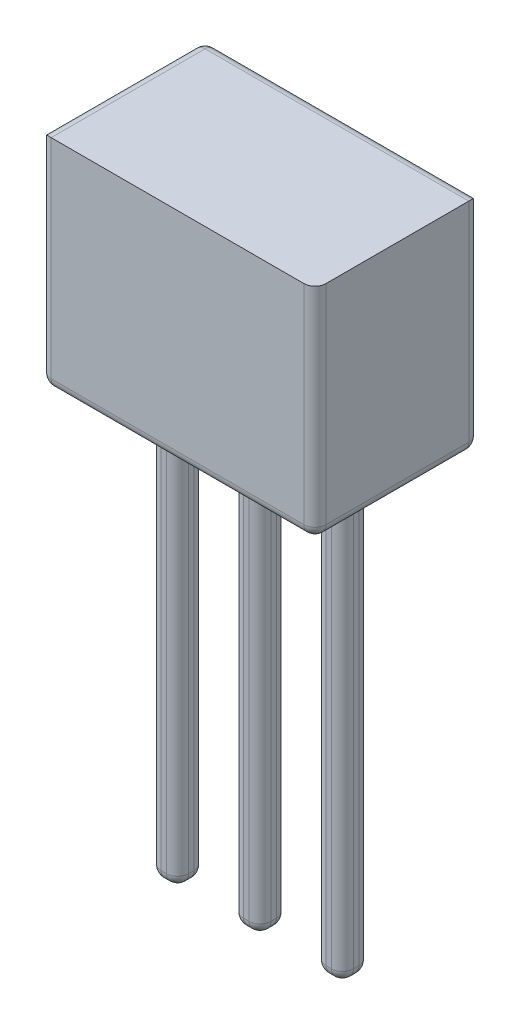
SolidWorks part; units mm, degrees
ref_plane "Front Plane" through (0, 0, 0) normal (0, 0, 1) x (1, 0, 0)
ref_plane "Top Plane" through (0, 0, 0) normal (0, 1, 0) x (1, 0, 0)
ref_plane "Right Plane" through (0, 0, 0) normal (1, 0, 0) x (0, 0, -1)
sketch "Sketch1" plane through (0, 0, 0) normal (0, 0, 1) x (1, 0, 0)
  line L1 (-50.1869, 22.1528) -> (-45.1869, 22.1528)
  line L2 (-50.1869, 22.1528) -> (-50.1869, 18.1528)
  line L3 (-50.1869, 18.1528) -> (-45.1869, 18.1528)
  line L4 (-45.1869, 22.1528) -> (-45.1869, 18.1528)
  line L5 (-50.1869, 22.1528) -> (-45.1869, 18.1528) construction
  line L6 (-50.1869, 18.1528) -> (-45.1869, 22.1528) construction
  point P0 (-47.6869, 20.1528)
  dimension "D1" = 4
  dimension "D2" = 5
extrude "Boss-Extrude1" add sketch "Sketch1" along normal blind 3
sketch "Sketch2" plane through (0, 18.1528, 0) normal (0, -1, 0) x (1, 0, 0)
  line L1 (-49.4369, 1.75) -> (-48.9369, 1.75)
  line L2 (-49.4369, 1.75) -> (-49.4369, 1.25)
  line L3 (-49.4369, 1.25) -> (-48.9369, 1.25)
  line L4 (-48.9369, 1.75) -> (-48.9369, 1.25)
  line L5 (-47.9369, 1.75) -> (-47.4369, 1.75)
  line L6 (-47.9369, 1.75) -> (-47.9369, 1.25)
  line L7 (-47.9369, 1.25) -> (-47.4369, 1.25)
  line L8 (-47.4369, 1.75) -> (-47.4369, 1.25)
  line L9 (-46.4369, 1.75) -> (-45.9369, 1.75)
  line L10 (-46.4369, 1.75) -> (-46.4369, 1.25)
  line L11 (-46.4369, 1.25) -> (-45.9369, 1.25)
  line L12 (-45.9369, 1.75) -> (-45.9369, 1.25)
  line L13 (-50.1869, 0) -> (-45.1869, 0) construction
  line L14 (-50.1869, 3) -> (-45.1869, 3) construction
  line L16 (-50.1869, 3) -> (-50.1869, 0) construction
  point P16 (-50.1869, 1.5)
  dimension "D1" = 0.5
  dimension "D2" = 0.5
  dimension "D3" = 1.25
  dimension "D4" = 1.25
  dimension "D5" = 1.25
  dimension "D6" = 1
  dimension "D7" = 1
  dimension "D8" = 0.75
extrude "Boss-Extrude2" add sketch "Sketch2" along normal blind 8
fillet "Fillet2" radius 0.2 46 edges at (-50.1869, 22.1528, 1.5) (-50.1869, 18.1528, 1.5) (-45.1869, 18.1528, 1.5) (-47.6869, 18.1528, 3) (-50.1869, 20.1528, 3) (-45.1869, 20.1528, 3) (-47.6869, 18.1528, 0) (-50.1869, 20.1528, 0) (-47.6869, 22.1528, 0) (-45.1869, 20.1528, 0) (-49.4369, 14.1528, 1.25) (-48.9369, 14.1528, 1.25) (-48.9369, 14.1528, 1.75) (-49.4369, 14.1528, 1.75) (-49.1869, 10.1528, 1.75) (-48.9369, 10.1528, 1.5) (-49.1869, 10.1528, 1.25) (-49.4369, 10.1528, 1.5) (-49.1869, 18.1528, 1.75) (-48.9369, 18.1528, 1.5) (-49.1869, 18.1528, 1.25) (-49.4369, 18.1528, 1.5) (-47.9369, 14.1528, 1.25) (-47.4369, 14.1528, 1.25) (-47.4369, 14.1528, 1.75) (-47.9369, 14.1528, 1.75) (-47.6869, 10.1528, 1.75) (-47.4369, 10.1528, 1.5) (-47.6869, 10.1528, 1.25) (-47.9369, 10.1528, 1.5) (-47.6869, 18.1528, 1.75) (-47.4369, 18.1528, 1.5) (-47.6869, 18.1528, 1.25) (-47.9369, 18.1528, 1.5) (-46.4369, 14.1528, 1.25) (-45.9369, 14.1528, 1.25) (-45.9369, 14.1528, 1.75) (-46.4369, 14.1528, 1.75) (-46.1869, 10.1528, 1.75) (-45.9369, 10.1528, 1.5) (-46.1869, 10.1528, 1.25) (-46.4369, 10.1528, 1.5) (-46.1869, 18.1528, 1.75) (-45.9369, 18.1528, 1.5) (-46.1869, 18.1528, 1.25) (-46.4369, 18.1528, 1.5)
